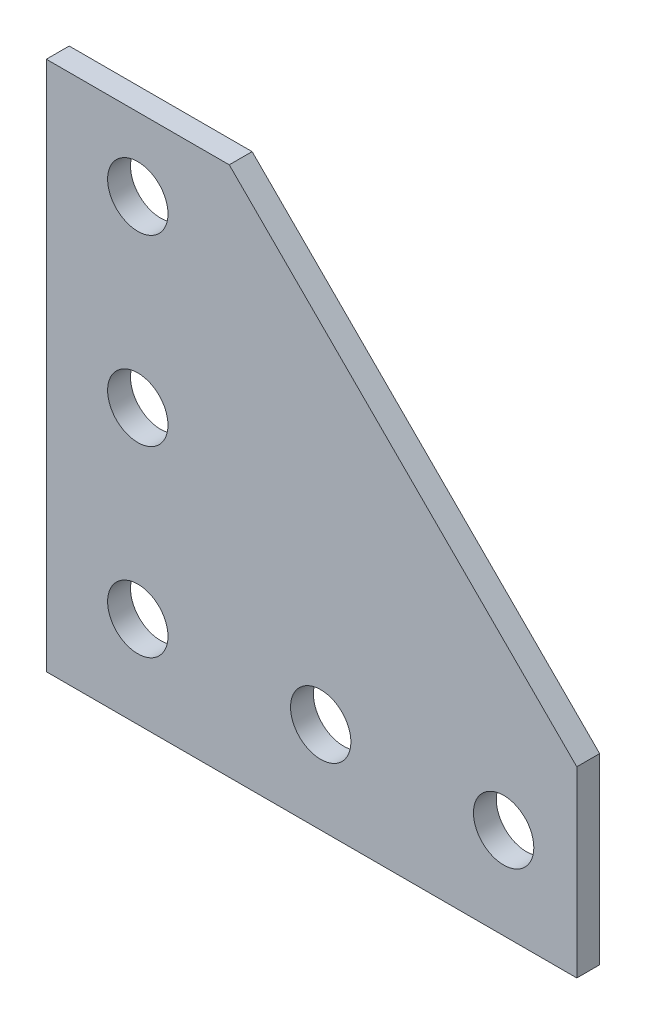
SolidWorks part; units mm, degrees
material "Chrome Stainless Steel"
ref_plane "Front Plane" through (0, 0, 0) normal (0, 0, 1) x (1, 0, 0)
ref_plane "Top Plane" through (0, 0, 0) normal (0, 1, 0) x (1, 0, 0)
ref_plane "Right Plane" through (0, 0, 0) normal (1, 0, 0) x (0, 0, -1)
sketch "Sketch1" plane through (0, 0, 0) normal (0, 0, 1) x (1, 0, 0)
  line L0 (-9, 29) -> (29, -9)
  line L1 (-29, 29) -> (-9, 29)
  line L2 (-29, 29) -> (-29, -29)
  line L3 (-29, -29) -> (29, -29)
  line L4 (29, -9) -> (29, -29)
  line L5 (-29, 29) -> (29, -29) construction
  line L6 (-29, -29) -> (10, 10) construction
  point P0 (0, 0)
  dimension "D1" = 58
  dimension "D2" = 58
  dimension "D3" = 20
  dimension "D4" = 20
extrude "Boss-Extrude1" add sketch "Sketch1" along normal blind 2.5
sketch "Sketch2" plane through (0, 0, 2.5) normal (0, 0, 1) x (1, 0, 0)
  line L0 (-29, 29) -> (-29, -29) construction
  line L1 (-29, -29) -> (29, -29) construction
  circle A0 centre (-19, -19) radius 3.3
  dimension "D1" = 6.6
  dimension "D2" = 10
  dimension "D3" = 10
extrude "Cut-Extrude1" cut sketch "Sketch2" against normal through all
pattern_linear "LPattern1" count 3 spacing 20 along (1, 0, 0) of "Cut-Extrude1"
pattern_linear "LPattern2" count 3 spacing 20 along (0, 1, 0) of "Cut-Extrude1"
